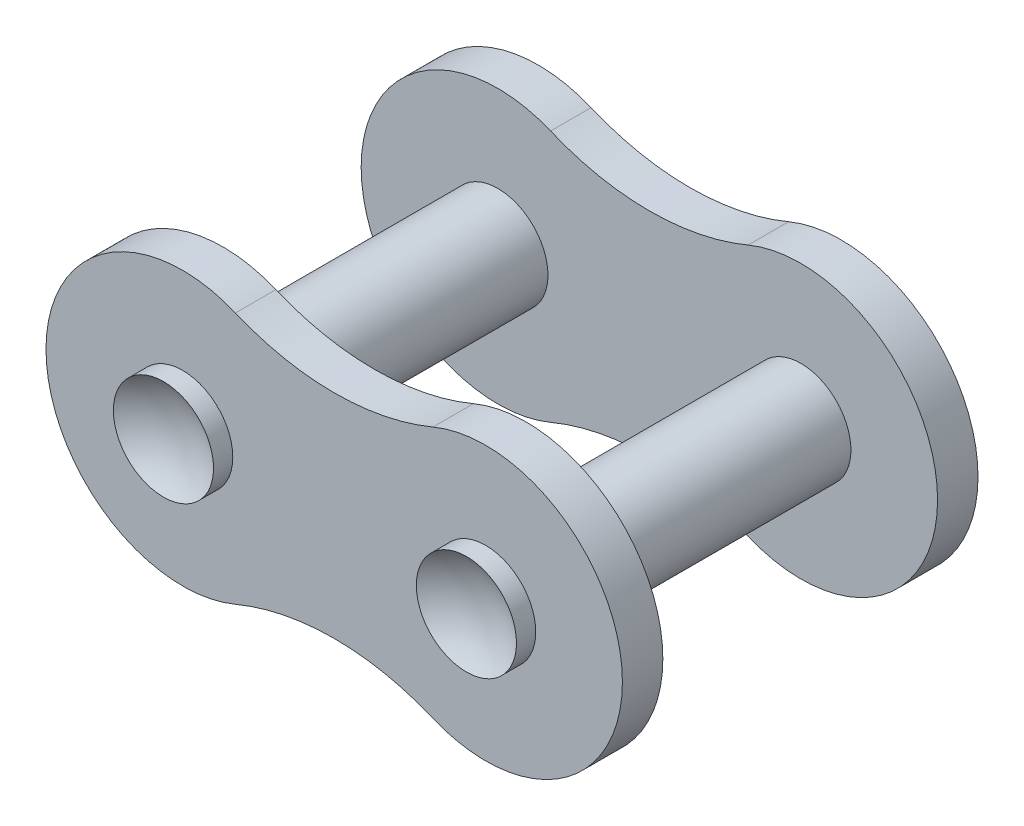
SolidWorks part; units mm, degrees
ref_plane "Front Plane" through (0, 0, 0) normal (0, 0, 1) x (1, 0, 0)
ref_plane "Top Plane" through (0, 0, 0) normal (0, 1, 0) x (1, 0, 0)
ref_plane "Right Plane" through (0, 0, 0) normal (1, 0, 0) x (0, 0, -1)
sketch "Sketch3" plane through (0, 0, 0) normal (0, 0, 1) x (1, 0, 0)
  line L0 (-5.9944, 0) -> (5.9944, 0) construction
  circle A0 centre (-5.9944, 0) radius 1.9812
  circle A1 centre (5.9944, 0) radius 1.9812
  point P4 (-6.2096, 0)
  point P8 (0, 0)
  dimension "D1" = 11.9888
  dimension "D2" = 3.9624
extrude "Boss-Extrude1" add sketch "Sketch3" along normal mid plane 15.5956
ref_plane "Plane1" through (0, 0, 7.0358) normal (0, 0, 1) x (1, 0, 0)
sketch "Sketch4" plane through (0, 0, 7.0358) normal (0, 0, 1) x (1, 0, 0)
  line L0 (-5.9944, 0) -> (5.9944, 0) construction
  arc A0 (-3.9081, 4.9918) -> (-3.9081, -4.9918) centre (-5.9944, 0) ccw
  arc A1 (3.9081, -4.9918) -> (3.9081, 4.9918) centre (5.9944, 0) ccw
  arc A2 (-3.9081, 4.9918) -> (3.9081, 4.9918) centre (0, 14.3425) ccw
  arc A3 (-3.9081, -4.9918) -> (3.9081, -4.9918) centre (0, -14.3425) cw
  dimension "D1" = 10.8204
  dimension "D2" = 10.1346
extrude "Boss-Extrude2" add sketch "Sketch4" against normal blind 1.6002
mirror "Mirror1" about plane through (0, 0, 0) normal (0, 0, 1) of "Boss-Extrude2"
sketch "Sketch5" plane through (0, 0, 0) normal (0, 1, 0) x (1, 0, 0)
  line L0 (-5.9944, -7.7978) -> (-5.9944, 7.7978) construction
  line L1 (-7.9756, -7.7978) -> (-4.0132, -7.7978) construction
  line L2 (-4.0132, 7.7978) -> (-7.9756, 7.7978) construction
  line L3 (-4.0132, -7.7978) -> (-4.0132, -7.0358) construction
  line L4 (0, -5.4356) -> (0, 5.4356) construction
  line L5 (-5.9944, 7.7978) -> (-5.9944, 7.1374)
  line L6 (-5.9944, -7.7978) -> (-5.9944, -7.1374)
  line L7 (-7.9756, -7.7978) -> (-4.0132, -7.7978)
  line L8 (3.9081, -5.4356) -> (-3.9081, -5.4356) construction
  line L9 (-3.9081, 5.4356) -> (3.9081, 5.4356) construction
  line L10 (-5.9944, 7.7978) -> (-4.0132, 7.7978)
  arc A0 (-5.9944, -7.1374) -> (-4.0132, -7.7978) centre (-5.9944, -10.4394) cw
  arc A4 (-5.9944, 7.1374) -> (-4.0132, 7.7978) centre (-5.9944, 10.4394) ccw
  dimension "D1" = 3.302
  dimension "D2" = 0.6604
  dimension "D3" = 0.6604
revolve "Cut-Revolve1" cut sketch "Sketch5" angle 360 about L0
mirror "Mirror2" about plane through (0, 0, 0) normal (1, 0, 0) of "Cut-Revolve1"
